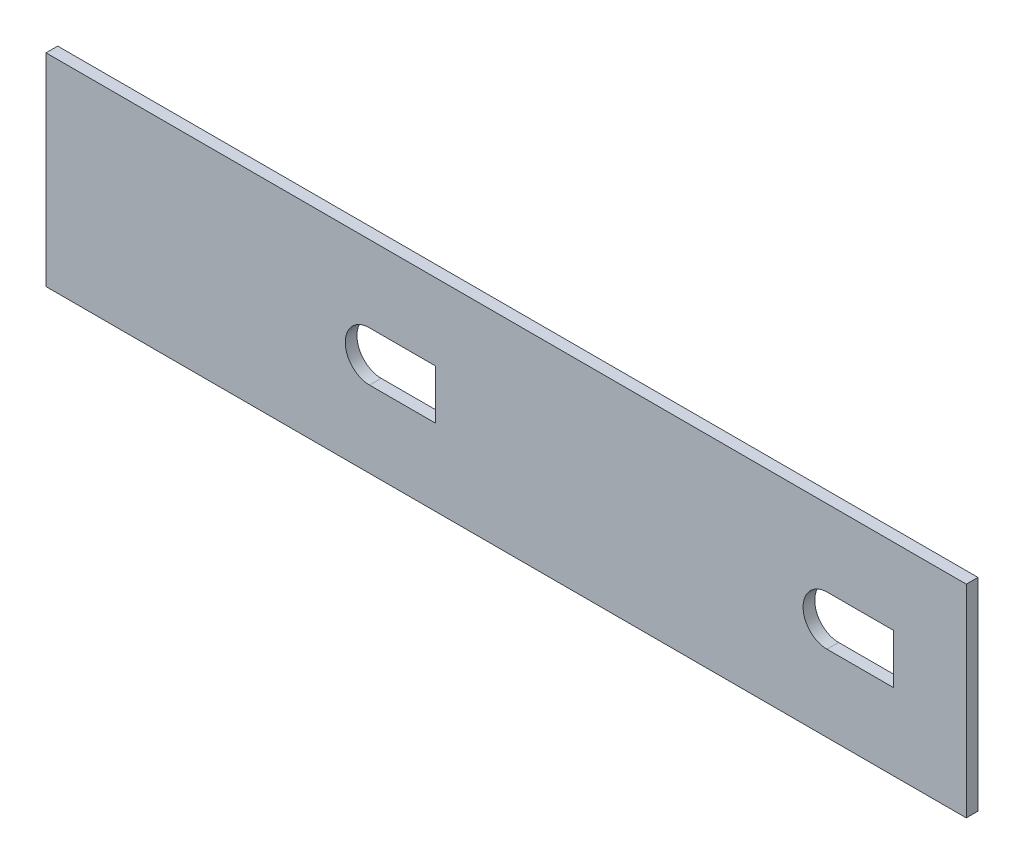
SolidWorks part; units mm, degrees
material "FiberBoard"
ref_plane "Front Plane" through (0, 0, 0) normal (0, 0, 1) x (1, 0, 0)
ref_plane "Top Plane" through (0, 0, 0) normal (0, 1, 0) x (1, 0, 0)
ref_plane "Right Plane" through (0, 0, 0) normal (1, 0, 0) x (0, 0, -1)
sketch "Sketch1" plane through (0, 0, 0) normal (0, 0, 1) x (1, 0, 0)
  line L0 (-366.5883, -417.4227) -> (-366.5883, 16.4781) construction
  line L1 (-116.5883, -45.8674) -> (-366.5883, -45.8674)
  line L2 (-116.5883, -45.8674) -> (-116.5883, 9.1326)
  line L3 (-116.5883, 9.1326) -> (-366.5883, 9.1326)
  line L4 (-366.5883, -45.8674) -> (-366.5883, 9.1326)
  line L5 (-366.5883, -417.4227) -> (-366.5883, 16.4781) construction
  line L6 (-360.2383, -18.3674) -> (-147.876, -18.3674) construction
  line L7 (-360.2383, -18.3674) -> (-147.876, -18.3674) construction
  line L8 (-147.876, -18.3674) -> (-116.5883, -18.3674) construction
  line L9 (-278.8074, -11.6353) -> (-260.8074, -11.6353)
  line L10 (-260.8074, -11.6353) -> (-260.8074, -25.0941)
  line L11 (-260.8074, -25.0941) -> (-278.7081, -25.0941)
  line L12 (-154.3603, -11.6353) -> (-136.3603, -11.6353)
  line L13 (-136.3603, -11.6353) -> (-136.3603, -25.0941)
  line L14 (-136.3603, -25.0941) -> (-154.4585, -25.0941)
  spline S0 degree 3 poles (-278.4749, -11.629) (-279.1319, -11.6398) (-279.3498, -11.6545) (-279.7834, -11.7064) (-280, -11.7438) (-280.637, -11.8882) (-281.0462, -12.0269) (-281.8342, -12.3872) (-282.2148, -12.6111) (-282.9129, -13.1226) (-283.2349, -13.4115) (-283.8244, -14.0566) (-284.0847, -14.4053) (-284.4209, -14.9594) (-284.5242, -15.1496) (-284.7128, -15.5413) (-284.7985, -15.7437) (-285.0233, -16.3561) (-285.1323, -16.774) (-285.271, -17.6286) (-285.2998, -18.0687) (-285.2763, -18.9342) (-285.2251, -19.3631) (-285.0869, -20.0004) (-285.0302, -20.2127) (-284.898, -20.627) (-284.8225, -20.8298) (-284.5682, -21.4252) (-284.362, -21.8051) (-283.8734, -22.5295) (-283.5966, -22.865) (-283.1392, -23.3229) (-282.9794, -23.4684) (-282.6447, -23.7444) (-282.4687, -23.8757) (-281.926, -24.2401) (-281.5455, -24.4442) (-280.7472, -24.7745) (-280.3242, -24.9013) (-279.4726, -25.0632) (-279.0424, -25.1001) (-278.3907, -25.09) (-278.1713, -25.0755) (-277.7391, -25.0243) (-277.5258, -24.9877) (-276.8937, -24.8458) (-276.4814, -24.7075) (-275.6858, -24.3447) (-275.3129, -24.1254) (-274.6143, -23.6148) (-274.286, -23.3199) (-273.7014, -22.6798) (-273.4424, -22.3337) (-273.1039, -21.7757) (-272.9992, -21.5824) (-272.811, -21.1906) (-272.7268, -20.9912) (-272.5037, -20.383) (-272.3935, -19.9629) (-272.2538, -19.0997) (-272.2259, -18.6679) (-272.243, -18.0199) (-272.2585, -17.8039) (-272.3101, -17.3717) (-272.3463, -17.155) (-272.4841, -16.5183) (-272.6146, -16.1071) (-272.9527, -15.3109) (-273.1629, -14.9229) (-273.6459, -14.2046) (-273.9195, -13.8708) (-274.3788, -13.4091) (-274.5411, -13.261) (-274.8767, -12.9838) (-275.0501, -12.8543) (-275.5872, -12.4927) (-275.9673, -12.2873) (-276.7747, -11.9527) (-277.1916, -11.8283) (-278.0394, -11.6667) (-278.4749, -11.629) (-279.1319, -11.6398) (-279.3498, -11.6545) knots -0.03125 -0.03125 0 0 0.015625 0.015625 0.03125 0.03125 0.0625 0.0625 0.09375 0.09375 0.125 0.125 0.15625 0.15625 0.171875 0.171875 0.1875 0.1875 0.21875 0.21875 0.25 0.25 0.28125 0.28125 0.296875 0.296875 0.3125 0.3125 0.34375 0.34375 0.375 0.375 0.390625 0.390625 0.40625 0.40625 0.4375 0.4375 0.46875 0.46875 0.5 0.5 0.515625 0.515625 0.53125 0.53125 0.5625 0.5625 0.59375 0.59375 0.625 0.625 0.65625 0.65625 0.671875 0.671875 0.6875 0.6875 0.71875 0.71875 0.75 0.75 0.765625 0.765625 0.78125 0.78125 0.8125 0.8125 0.84375 0.84375 0.875 0.875 0.890625 0.890625 0.90625 0.90625 0.9375 0.9375 0.96875 0.96875 1 1 1.015625 1.015625 1.03125 only from (-278.9129, -11.6362) to (-278.9129, -11.6362) construction
  spline S1 degree 3 poles (-153.8157, -11.6434) (-154.6917, -11.629) (-155.1229, -11.6662) (-155.7597, -11.7871) (-155.9702, -11.8384) (-156.388, -11.9632) (-156.5949, -12.0369) (-157.1963, -12.2861) (-157.5768, -12.4909) (-158.1173, -12.8548) (-158.2932, -12.9864) (-158.6288, -13.264) (-158.7888, -13.4101) (-159.2462, -13.8699) (-159.5213, -14.2048) (-160.0092, -14.9316) (-160.2147, -15.3125) (-160.4678, -15.9089) (-160.5429, -16.112) (-160.6742, -16.5266) (-160.7305, -16.739) (-160.8676, -17.3766) (-160.9181, -17.8055) (-160.9406, -18.6708) (-160.9114, -19.1109) (-160.7723, -19.965) (-160.6632, -20.3823) (-160.439, -20.9933) (-160.3534, -21.1956) (-160.1645, -21.588) (-160.0611, -21.7783) (-159.7251, -22.332) (-159.4667, -22.6783) (-158.8778, -23.3228) (-158.5534, -23.6137) (-158.0311, -23.9958) (-157.8506, -24.1145) (-157.4765, -24.3341) (-157.2815, -24.4356) (-156.6868, -24.7068) (-156.2775, -24.8444) (-155.4336, -25.0346) (-154.9948, -25.0864) (-154.1288, -25.1002) (-153.698, -25.0638) (-153.0553, -24.9418) (-152.8419, -24.8897) (-152.4262, -24.7654) (-152.0187, -24.6204) (-151.6277, -24.4353) (-151.2448, -24.23) (-151.0565, -24.1166) (-150.5143, -23.7522) (-150.181, -23.4768) (-149.5686, -22.8636) (-149.2884, -22.5228) (-148.8048, -21.8049) (-148.5982, -21.4254) (-148.3421, -20.8246) (-148.2657, -20.6186) (-148.1341, -20.2046) (-148.0786, -19.9956) (-147.9416, -19.3625) (-147.8898, -18.9319) (-147.8669, -18.0574) (-147.896, -17.6258) (-147.9998, -16.9866) (-148.0446, -16.7749) (-148.1548, -16.3545) (-148.2207, -16.1447) (-148.4462, -15.5325) (-148.6338, -15.1437) (-149.0824, -14.4045) (-149.347, -14.051) (-149.9316, -13.412) (-150.2526, -13.1234) (-150.7781, -12.7384) (-150.9618, -12.6175) (-151.3373, -12.3971) (-151.5294, -12.2972) (-152.1183, -12.0278) (-152.5278, -11.8885) (-153.3825, -11.6949) (-153.8157, -11.6434) (-154.6917, -11.629) (-155.1229, -11.6662) knots -0.03125 -0.03125 0 0 0.03125 0.03125 0.046875 0.046875 0.0625 0.0625 0.09375 0.09375 0.109375 0.109375 0.125 0.125 0.15625 0.15625 0.1875 0.1875 0.203125 0.203125 0.21875 0.21875 0.25 0.25 0.28125 0.28125 0.3125 0.3125 0.328125 0.328125 0.34375 0.34375 0.375 0.375 0.40625 0.40625 0.421875 0.421875 0.4375 0.4375 0.46875 0.46875 0.5 0.5 0.53125 0.53125 0.546875 0.546875 0.5625 0.578125 0.578125 0.59375 0.59375 0.625 0.625 0.65625 0.65625 0.6875 0.6875 0.703125 0.703125 0.71875 0.71875 0.75 0.75 0.78125 0.78125 0.796875 0.796875 0.8125 0.8125 0.84375 0.84375 0.875 0.875 0.90625 0.90625 0.921875 0.921875 0.9375 0.9375 0.96875 0.96875 1 1 1.03125 1.03125 1.046875 only from (-154.2537, -11.6362) to (-154.2537, -11.6362) construction
  spline S2 degree 3 poles (-278.8074, -11.6353) (-278.8426, -11.6353) (-278.8777, -11.6356) (-279.1319, -11.6398) (-279.3498, -11.6545) (-279.7834, -11.7064) (-280, -11.7438) (-280.637, -11.8882) (-281.0462, -12.0269) (-281.8342, -12.3872) (-282.2148, -12.6111) (-282.9129, -13.1226) (-283.2349, -13.4115) (-283.8244, -14.0566) (-284.0847, -14.4053) (-284.4209, -14.9594) (-284.5242, -15.1496) (-284.7128, -15.5413) (-284.7985, -15.7437) (-285.0233, -16.3561) (-285.1323, -16.774) (-285.271, -17.6286) (-285.2998, -18.0687) (-285.2763, -18.9342) (-285.2251, -19.3631) (-285.0869, -20.0004) (-285.0302, -20.2127) (-284.898, -20.627) (-284.8225, -20.8298) (-284.5682, -21.4252) (-284.362, -21.8051) (-283.8734, -22.5295) (-283.5966, -22.865) (-283.1392, -23.3229) (-282.9794, -23.4684) (-282.6447, -23.7444) (-282.4687, -23.8757) (-281.926, -24.2401) (-281.5455, -24.4442) (-280.7472, -24.7745) (-280.3242, -24.9013) (-279.5053, -25.0569) (-279.1085, -25.0941) (-278.7081, -25.0941) knots 0.997491 0.997491 0.997491 0.997491 1 1 1.015625 1.015625 1.03125 1.03125 1.0625 1.0625 1.09375 1.09375 1.125 1.125 1.15625 1.15625 1.171875 1.171875 1.1875 1.1875 1.21875 1.21875 1.25 1.25 1.28125 1.28125 1.296875 1.296875 1.3125 1.3125 1.34375 1.34375 1.375 1.375 1.390625 1.390625 1.40625 1.40625 1.4375 1.4375 1.46875 1.46875 1.497598 1.497598 1.497598 1.497598
  spline S3 degree 3 poles (-154.3603, -11.6353) (-154.7617, -11.6353) (-155.1574, -11.6727) (-155.7597, -11.7871) (-155.9702, -11.8384) (-156.388, -11.9632) (-156.5949, -12.0369) (-157.1963, -12.2861) (-157.5768, -12.4909) (-158.1173, -12.8548) (-158.2932, -12.9864) (-158.6288, -13.264) (-158.7888, -13.4101) (-159.2462, -13.8699) (-159.5213, -14.2048) (-160.0092, -14.9316) (-160.2147, -15.3125) (-160.4678, -15.9089) (-160.5429, -16.112) (-160.6742, -16.5266) (-160.7305, -16.739) (-160.8676, -17.3766) (-160.9181, -17.8055) (-160.9406, -18.6708) (-160.9114, -19.1109) (-160.7723, -19.965) (-160.6632, -20.3823) (-160.439, -20.9933) (-160.3534, -21.1956) (-160.1645, -21.588) (-160.0611, -21.7783) (-159.7251, -22.332) (-159.4667, -22.6783) (-158.8778, -23.3228) (-158.5534, -23.6137) (-158.0311, -23.9958) (-157.8506, -24.1145) (-157.4765, -24.3341) (-157.2815, -24.4356) (-156.6868, -24.7068) (-156.2775, -24.8444) (-155.4336, -25.0346) (-154.9948, -25.0864) (-154.5274, -25.0939) (-154.4929, -25.0941) (-154.4585, -25.0941) knots 0.002539 0.002539 0.002539 0.002539 0.03125 0.03125 0.046875 0.046875 0.0625 0.0625 0.09375 0.09375 0.109375 0.109375 0.125 0.125 0.15625 0.15625 0.1875 0.1875 0.203125 0.203125 0.21875 0.21875 0.25 0.25 0.28125 0.28125 0.3125 0.3125 0.328125 0.328125 0.34375 0.34375 0.375 0.375 0.40625 0.40625 0.421875 0.421875 0.4375 0.4375 0.46875 0.46875 0.5 0.5 0.502487 0.502487 0.502487 0.502487
  point P8 (-116.5883, -18.3674)
  dimension "D1" = 55
  dimension "D2" = 250
  dimension "D3" = 18
  dimension "D4" = 17.9006
  dimension "D5" = 18
extrude "Boss-Extrude1" add sketch "Sketch1" along normal blind 3.175
